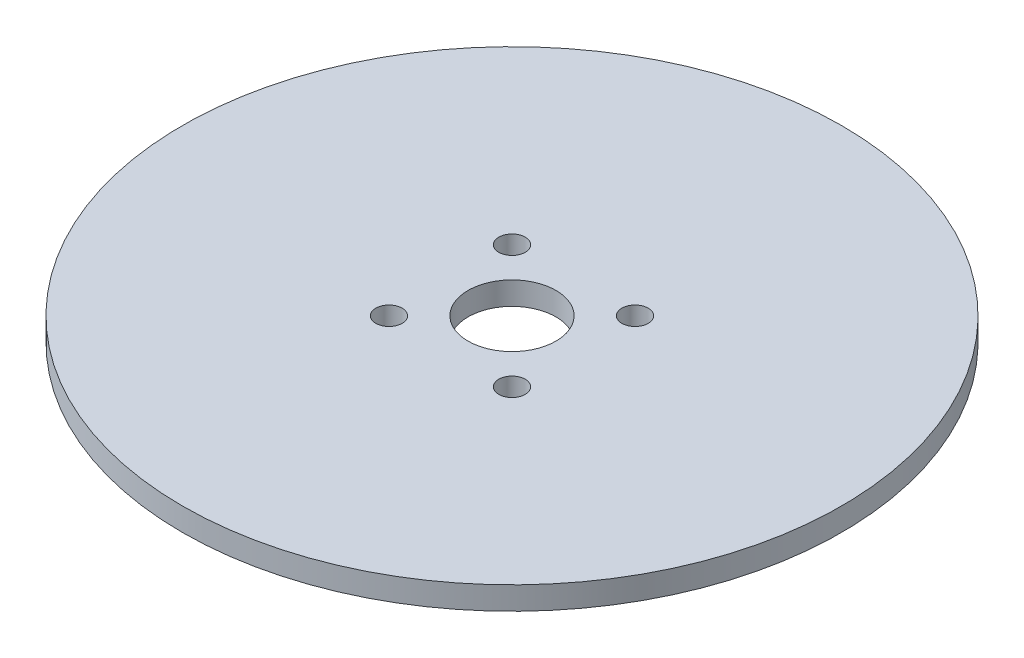
SolidWorks part; units mm, degrees
ref_plane "Front Plane" through (0, 0, 0) normal (0, 0, 1) x (1, 0, 0)
ref_plane "Top Plane" through (0, 0, 0) normal (0, 1, 0) x (1, 0, 0)
ref_plane "Right Plane" through (0, 0, 0) normal (1, 0, 0) x (0, 0, -1)
sketch "Sketch1" plane through (0, 0, 0) normal (0, 1, 0) x (1, 0, 0)
  circle A0 centre (0, 0) radius 37.5
  dimension "D1" = 75
extrude "Boss-Extrude1" add sketch "Sketch1" along normal blind 2.61
sketch "Sketch2" plane through (0, 2.61, 0) normal (0, 1, 0) x (1, 0, 0)
  circle A0 centre (0, 0) radius 5
  dimension "D1" = 10
extrude "Cut-Extrude1" cut sketch "Sketch2" against normal blind 13.05
sketch "Sketch3" plane through (0, 2.61, 0) normal (0, 1, 0) x (1, 0, 0)
  line L1 (-7, 7) -> (7, 7) construction
  line L2 (-7, 7) -> (-7, -7) construction
  line L3 (-7, -7) -> (7, -7) construction
  line L4 (7, 7) -> (7, -7) construction
  circle A1 centre (-7, 7) radius 1.5
  circle A2 centre (7, 7) radius 1.5
  circle A3 centre (7, -7) radius 1.5
  circle A4 centre (-7, -7) radius 1.5
  dimension "D5" = 3
  dimension "D6" = 3
  dimension "D7" = 3
  dimension "D8" = 3
  dimension "D1" = 7
  dimension "D2" = 7
  dimension "D3" = 7
  dimension "D4" = 7
extrude "Cut-Extrude2" cut sketch "Sketch3" against normal through all
